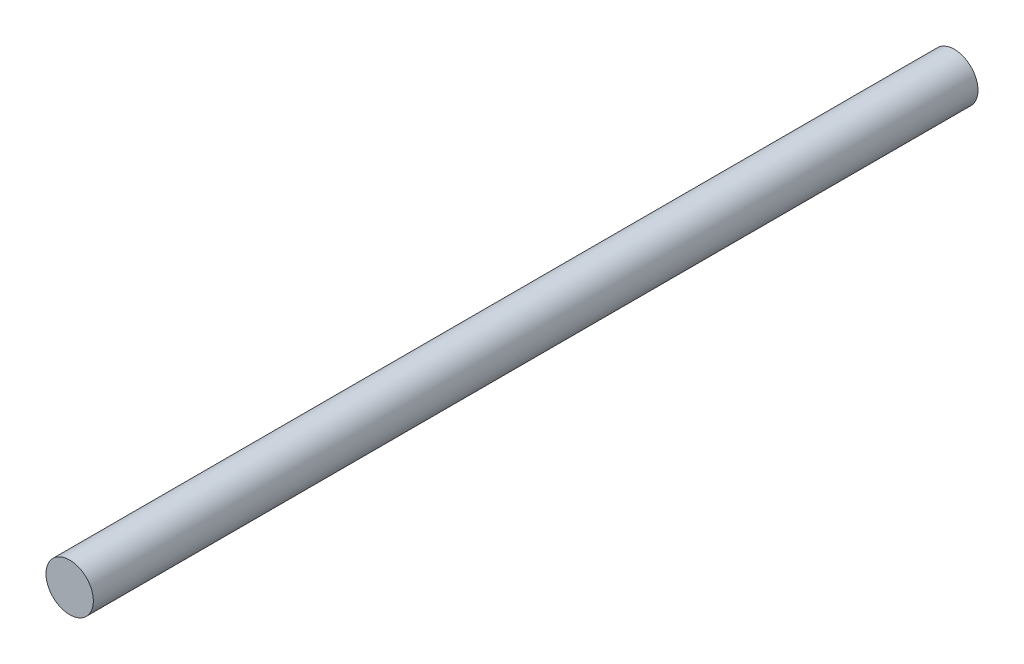
SolidWorks part; units mm, degrees
material "Plain Carbon Steel"
ref_plane "Front Plane" through (0, 0, 0) normal (0, 0, 1) x (1, 0, 0)
ref_plane "Top Plane" through (0, 0, 0) normal (0, 1, 0) x (1, 0, 0)
ref_plane "Right Plane" through (0, 0, 0) normal (1, 0, 0) x (0, 0, -1)
sketch "Sketch1" plane through (0, 0, 0) normal (0, 0, 1) x (1, 0, 0)
  circle A0 centre (0, 0) radius 9.525
  dimension "D1" = 19.05
extrude "Boss-Extrude1" add sketch "Sketch1" along normal blind 355.6
